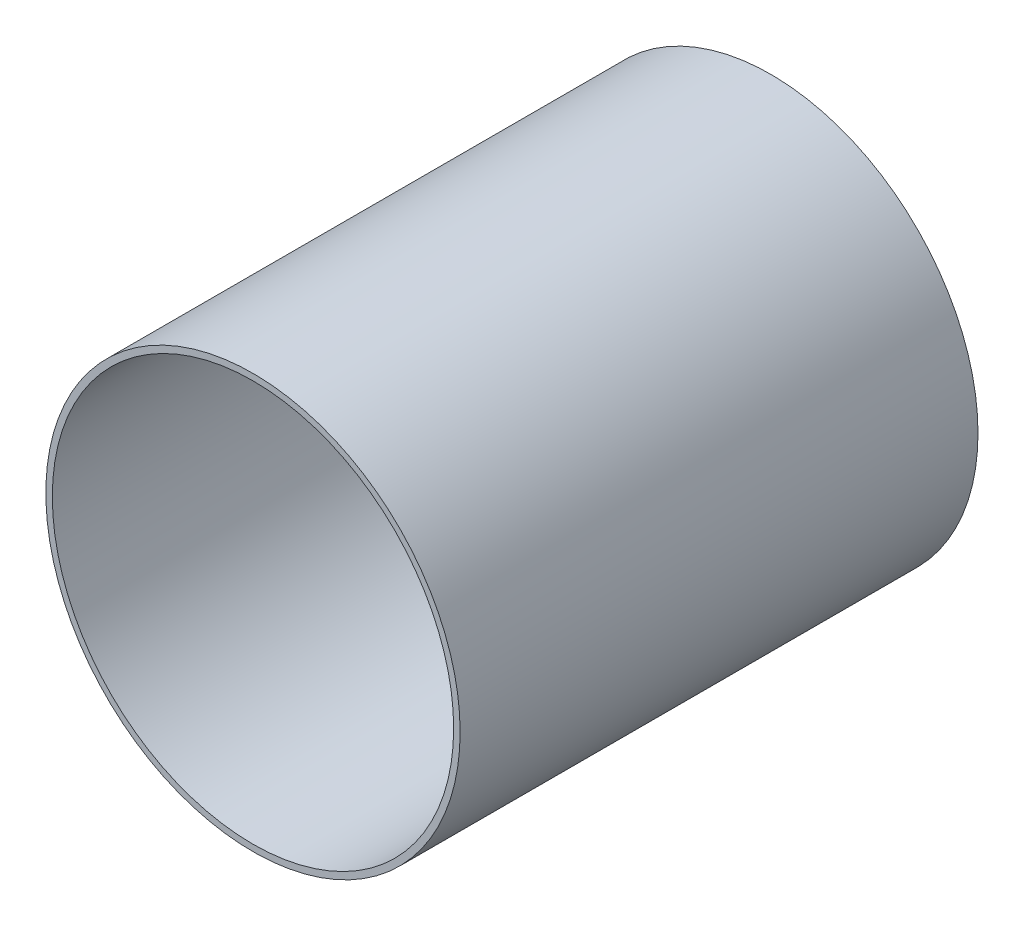
SolidWorks part; units mm, degrees
ref_plane "Plan de face" through (0, 0, 0) normal (0, 0, 1) x (1, 0, 0)
ref_plane "Plan de dessus" through (0, 0, 0) normal (0, 1, 0) x (1, 0, 0)
ref_plane "Plan de droite" through (0, 0, 0) normal (1, 0, 0) x (0, 0, -1)
sketch "Esquisse3" plane through (0, 0, 0) normal (0, 0, 1) x (1, 0, 0)
  circle A0 centre (0, 0) radius 80
  dimension "D1" = 160
extrude "Boss.-Extru.2" add sketch "Esquisse3" along normal blind 200
sketch "Esquisse4" plane through (0, 0, 200) normal (0, 0, 1) x (1, 0, 0)
  circle A0 centre (0, 0) radius 77.5
  dimension "D1" = 155
extrude "Enlèv. mat.-Extru.2" cut sketch "Esquisse4" against normal blind 195
